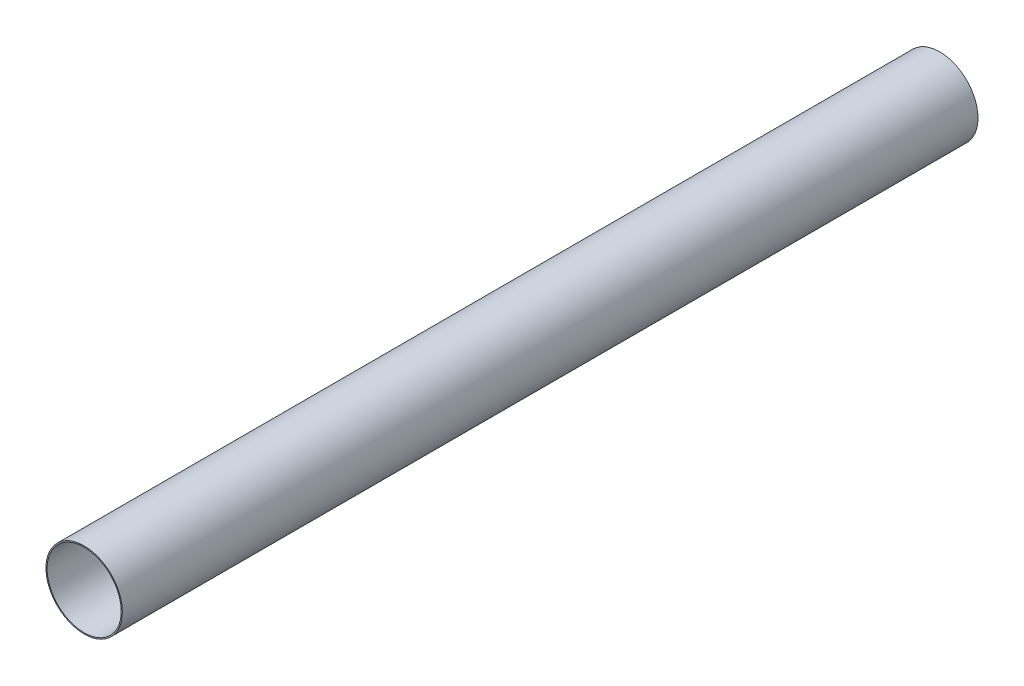
SolidWorks part; units mm, degrees
ref_plane "Front Plane" through (0, 0, 0) normal (0, 0, 1) x (1, 0, 0)
ref_plane "Top Plane" through (0, 0, 0) normal (0, 1, 0) x (1, 0, 0)
ref_plane "Right Plane" through (0, 0, 0) normal (1, 0, 0) x (0, 0, -1)
sketch "Sketch1" plane through (0, 0, 0) normal (0, 0, 1) x (1, 0, 0)
  circle A0 centre (0, 0) radius 49.53
  circle A1 centre (0, 0) radius 51.054
  dimension "D1" = 99.06
  dimension "D2" = 102.108
extrude "Boss-Extrude1" add sketch "Sketch1" along normal blind 1143
